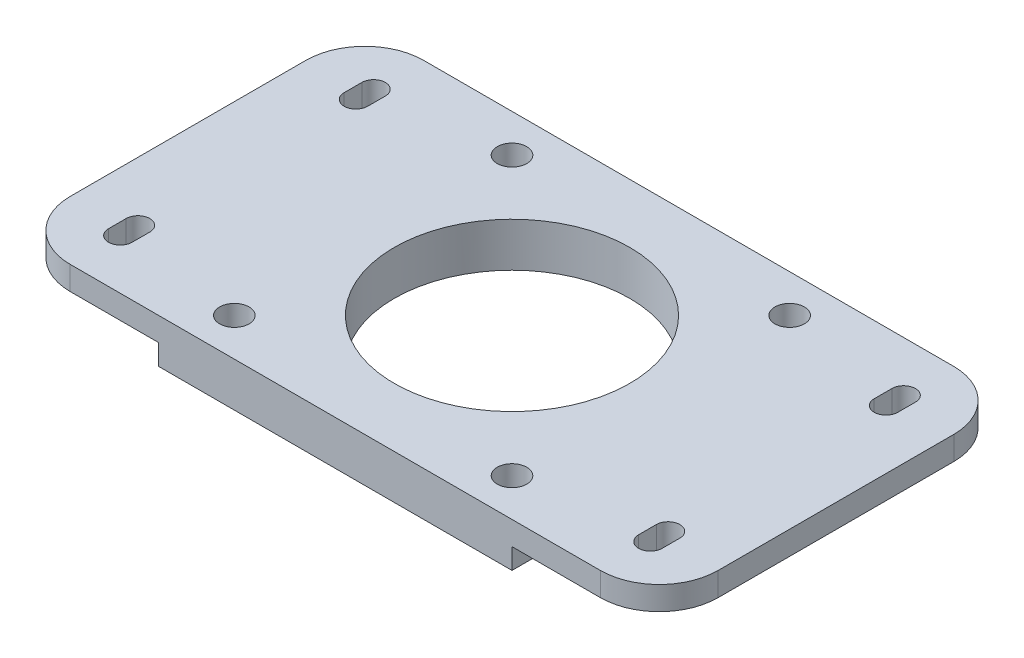
SolidWorks part; units mm, degrees
ref_plane "Front Plane" through (0, 0, 0) normal (0, 0, 1) x (1, 0, 0)
ref_plane "Top Plane" through (0, 0, 0) normal (0, 1, 0) x (1, 0, 0)
ref_plane "Right Plane" through (0, 0, 0) normal (1, 0, 0) x (0, 0, -1)
sketch "Sketch1" plane through (0, 0, 0) normal (0, 1, 0) x (1, 0, 0)
  line L1 (-30, -30) -> (30, -30)
  line L2 (-30, -30) -> (-30, 30)
  line L3 (-30, 30) -> (30, 30)
  line L4 (30, -30) -> (30, 30)
  line L5 (-30, -30) -> (30, 30) construction
  line L6 (-30, 30) -> (30, -30) construction
  circle A0 centre (0, 0) radius 20
  dimension "D3" = 40
  dimension "D1" = 60
  dimension "D2" = 60
extrude "Boss-Extrude1" add sketch "Sketch1" along normal blind 3.5
sketch "Sketch2" plane through (0, 3.5, -3.5) normal (0, -1, 0) x (1, 0, 0)
  line L0 (45, -26.5) -> (-45, -26.5)
  line L1 (-55, -16.5) -> (-55, 23.5)
  line L2 (-45, 33.5) -> (45, 33.5)
  line L3 (0, 33.5) -> (0, -26.5) construction
  line L6 (-45, -15) -> (-45, -18) construction
  line L7 (-47, -15) -> (-47, -18)
  line L8 (-55, 3.5) -> (71.16, 3.5) construction
  line L9 (-43, -18) -> (-43, -15)
  line L10 (-45, 22) -> (-45, 25) construction
  line L11 (-43, 25) -> (-43, 22)
  line L12 (-47, 22) -> (-47, 25)
  line L13 (55, -16.5) -> (55, 23.5)
  line L14 (45, -15) -> (45, -18) construction
  line L15 (43, -18) -> (43, -15)
  line L16 (47, -15) -> (47, -18)
  line L17 (45, 22) -> (45, 25) construction
  line L18 (47, 22) -> (47, 25)
  line L19 (43, 25) -> (43, 22)
  line L20 (-30, 33.5) -> (30, 33.5) construction
  line L21 (30, -26.5) -> (-30, -26.5) construction
  line L22 (-30, 33.5) -> (30, 33.5) construction
  arc A0 (-45, -26.5) -> (-55, -16.5) centre (-45, -16.5) cw
  arc A1 (-55, 23.5) -> (-45, 33.5) centre (-45, 23.5) cw
  arc A2 (-43, -15) -> (-47, -15) centre (-45, -15) ccw
  arc A3 (-47, -18) -> (-43, -18) centre (-45, -18) ccw
  arc A4 (-47, 25) -> (-43, 25) centre (-45, 25) cw
  arc A5 (-43, 22) -> (-47, 22) centre (-45, 22) cw
  arc A6 (45, -26.5) -> (55, -16.5) centre (45, -16.5) ccw
  arc A7 (55, 23.5) -> (45, 33.5) centre (45, 23.5) ccw
  arc A8 (47, -18) -> (43, -18) centre (45, -18) cw
  arc A9 (43, -15) -> (47, -15) centre (45, -15) cw
  arc A10 (43, 22) -> (47, 22) centre (45, 22) ccw
  arc A11 (47, 25) -> (43, 25) centre (45, 25) ccw
  circle A12 centre (0, 3.5) radius 20 construction
  circle A13 centre (0, 3.5) radius 20
  point P13 (-55, 33.5)
  dimension "D2" = 10
  dimension "D3" = 2
  dimension "D1" = 55
  dimension "D4" = 3
extrude "Boss-Extrude2" add sketch "Sketch2" against normal blind 4
hole_wizard "Ø5.0 (5) Diameter Hole1" positions "Sketch3" profile "Sketch4" hole size "Ø5.0" standard "ANSI Metric"
sketch "Sketch3" plane through (233.2982, 0, -449.6025) normal (0, -1, 0) x (-1, 0, 0)
  point P0 (256.8682, -473.1725)
  point P3 (209.7282, -473.1725)
  point P6 (209.7282, -426.0325)
  point P9 (256.8682, -426.0325)
sketch "Sketch4" plane through (-23.57, 0, 23.57) normal (1, 0, 0) x (0, 0, -1)
  line L0 (0, 0) -> (0, 26.5022)
  line L1 (0, 26.5022) -> (2.5, 25)
  line L2 (2.5, 25) -> (2.5, 0)
  line L3 (2.5, 0) -> (0, 0)
  line L4 (0, 26.5022) -> (-2.5, 25) construction
  line L5 (0, -6.35) -> (0, 107.95) construction
  dimension "Hole Dia." = 5
  dimension "Hole Depth" = 25
  dimension "Drill Angle" = 118
